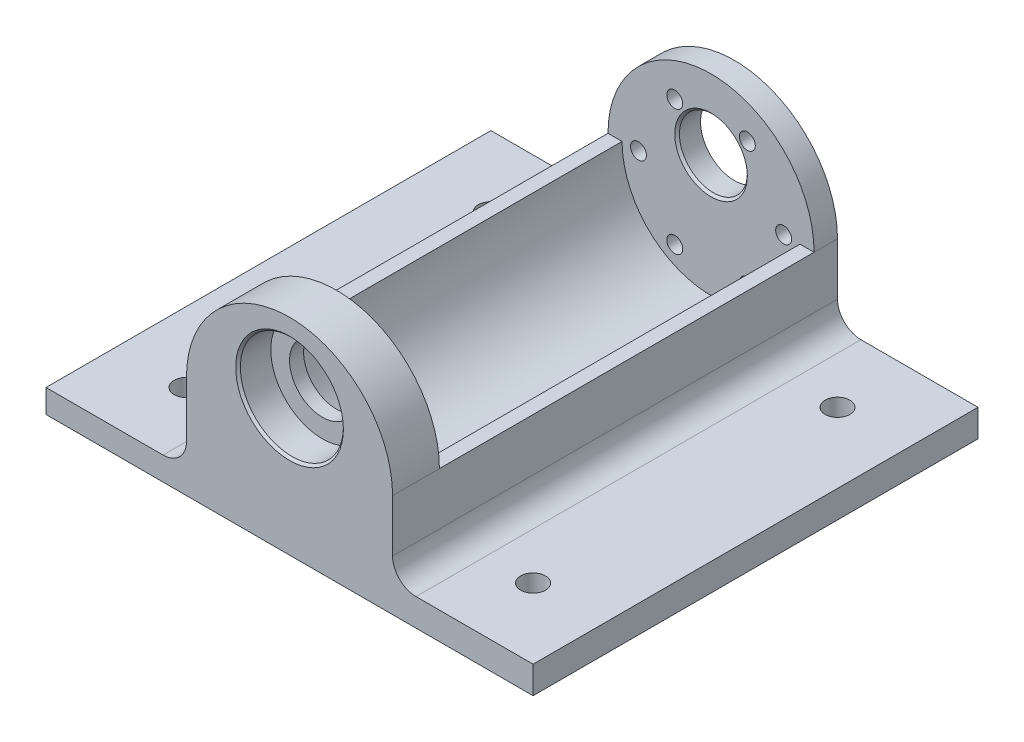
SolidWorks part; units mm, degrees
material "ABS"
ref_plane "Front Plane" through (0, 0, 0) normal (0, 0, 1) x (1, 0, 0)
ref_plane "Top Plane" through (0, 0, 0) normal (0, 1, 0) x (1, 0, 0)
ref_plane "Right Plane" through (0, 0, 0) normal (1, 0, 0) x (0, 0, -1)
sketch "Sketch3" plane through (0, 0, 0) normal (0, 0, 1) x (1, 0, 0)
  line L0 (0, 0) -> (0, 7) construction
  line L2 (22, 0) -> (22, -22)
  line L3 (-22, 0) -> (-22, -22)
  line L4 (22, -22) -> (-22, -22)
  arc A0 (22, 0) -> (-22, 0) centre (0, 0) ccw
  circle A1 centre (0, 0) radius 18.5 construction
  circle A2 centre (0, 0) radius 15.5 construction
  circle A3 centre (0, 7) radius 7.25
  dimension "D1" = 44
  dimension "D2" = 37
  dimension "D3" = 31
  dimension "D5" = 14.5
  dimension "D4" = 7
extrude "Boss-Extrude1" add sketch "Sketch3" along normal blind 5 contours A3 | A0 L3 L4 L2
hole_wizard "M3 Clearance Hole1" positions "Sketch5" profile "Sketch6" hole size "M3" standard "ISO" end condition through all
sketch "Sketch5" plane through (0, 0, 0) normal (0, 0, -1) x (-1, 0, 0)
  circle A0 centre (0, 0) radius 15.5 construction
  point P0 (-15.5, 0)
  point P5 (15.5, 0)
  point P7 (7.75, 13.4234)
  point P9 (-7.75, 13.4234)
  point P11 (-7.75, -13.4234)
  point P13 (7.75, -13.4234)
  dimension "D1" = 31
  dimension "D2" = 15.5
sketch "Sketch6" plane through (15.5, 0, 0) normal (1, 0, 0) x (0, 1, 0)
  line L0 (0, 0) -> (0, 5)
  line L1 (0, 5) -> (1.7, 5)
  line L2 (1.7, 5) -> (1.7, 0.025)
  line L3 (1.7, 0.025) -> (1.725, 0)
  line L5 (1.725, 0) -> (0, 0)
  line L6 (-1.7, 0.025) -> (-1.725, 0) construction
  line L11 (0, -6.35) -> (0, 107.95) construction
  dimension "Thru Hole Dia." = 3.4
  dimension "Thru Hole Depth" = 5
  dimension "Near C'Sink Dia." = 3.45
  dimension "Near C'Sink Angle" = 90
sketch "Sketch7" plane through (0, 0, 5) normal (0, 0, 1) x (1, 0, 0)
  line L0 (-19, 0) -> (-22, 0)
  line L1 (19, 0) -> (22, 0)
  line L2 (-22, 0) -> (-22, -22) construction
  line L3 (22, -22) -> (-22, -22) construction
  line L4 (22, 0) -> (22, -22) construction
  line L5 (-22, 0) -> (-22, -22)
  line L6 (22, -22) -> (-22, -22)
  line L7 (22, 0) -> (22, -22)
  circle A0 centre (0, 0) radius 19 construction
  arc A1 (-19, 0) -> (19, 0) centre (0, 0) ccw
  dimension "D1" = 38
extrude "Boss-Extrude2" add sketch "Sketch7" along normal blind 80
sketch "Sketch9" plane through (0, 0, 85) normal (0, 0, 1) x (1, 0, 0)
  line L0 (22, 0) -> (22, -22) construction
  line L1 (22, -22) -> (-22, -22) construction
  line L2 (-22, 0) -> (-22, -22) construction
  line L3 (22, 0) -> (22, -22)
  line L4 (22, -22) -> (-22, -22)
  line L5 (-22, 0) -> (-22, -22)
  arc A1 (22, 0) -> (-22, 0) centre (0, 0) ccw construction
  arc A2 (22, 0) -> (-22, 0) centre (0, 0) ccw
extrude "Boss-Extrude3" add sketch "Sketch9" along normal blind 10 contours L3 L4 L5 A2
sketch "Sketch16" plane through (0, 0, 95) normal (0, 0, 1) x (1, 0, 0)
  circle A1 centre (0, 7) radius 7.25 construction
  circle A2 centre (0, 7) radius 11
  circle A5 centre (0, 7) radius 7.25 construction
  dimension "D1" = 22
  dimension "D2" = 14.5
extrude "Cut-Extrude1" cut sketch "Sketch16" against normal blind 7
sketch "Sketch17" plane through (0, 0, 88) normal (0, 0, 1) x (1, 0, 0)
  circle A2 centre (0, 7) radius 7
  circle A3 centre (0, 7) radius 7.25 construction
  dimension "D1" = 14
extrude "Cut-Extrude2" cut sketch "Sketch17" against normal up to next contours A2
chamfer "Chamfer2" distance 0.5 angle 45 1 edges at (11, 7, 95)
chamfer "Chamfer3" distance 0.5 angle 45 1 edges at (7.25, 7, 5)
sketch "Sketch18" plane through (22, 0, 0) normal (1, 0, 0) x (0, 0, -1)
  line L0 (-95, -22) -> (0, -22)
  line L1 (-95, -22) -> (-95, -16.1617)
  line L2 (0, -22) -> (0, -16.1617)
  line L3 (-95, -16.1617) -> (0, -16.1617)
  dimension "D1" = 5.8383
extrude "Boss-Extrude5" add sketch "Sketch18" along normal blind 30
sketch "Sketch21" plane through (-22, 0, 0) normal (-1, 0, 0) x (0, 0, 1)
  line L0 (95, 0) -> (95, -22) construction
  line L1 (0, -22) -> (95, -22)
  line L2 (0, -22) -> (0, -17)
  line L3 (0, -17) -> (95, -17)
  line L4 (95, -22) -> (95, -17)
  dimension "D1" = 5
extrude "Boss-Extrude6" add sketch "Sketch21" along normal blind 30
fillet "Fillet1" radius 5 2 edges at (-22, -17, 47.5) (22, -16.1617, 47.5)
hole_wizard "M5 Clearance Slot1" positions "Sketch23" profile "Sketch22" size "M5" standard "ANSI Metric" slot yes end condition through all
sketch "Sketch23" plane through (0, -22, 0) normal (0, -1, 0) x (-1, 0, 0)
  line L1 (52, 0) -> (52, -95) construction
  line L2 (-52, -95) -> (-52, 0) construction
  line L4 (52, -80) -> (-52, -80) construction
  line L7 (-52, -15) -> (52, -15) construction
  line L10 (37, -95) -> (37, 0) construction
  line L11 (-52, -95) -> (52, -95) construction
  line L12 (-52, 0) -> (52, 0) construction
  line L15 (-37, -95) -> (-37, 0) construction
  point P0 (37, -80)
  point P2 (-37, -80)
  point P4 (-37, -15)
  point P6 (37, -15)
  dimension "D1" = 15
  dimension "D2" = 15
  dimension "D3" = 15
  dimension "D4" = 15
sketch "Sketch22" plane through (-37, -22, 80) normal (1, 0, 0) x (0, 0, -1)
  line L0 (0, 0) -> (0, 44)
  line L1 (0, 44) -> (2.65, 44)
  line L2 (2.65, 44) -> (2.65, 0)
  line L5 (2.65, 0) -> (0, 0)
  line L11 (0, -6.35) -> (0, 107.95) construction
  dimension "Thru Hole Dia." = 5.3
  dimension "Thru Hole Depth" = 44
